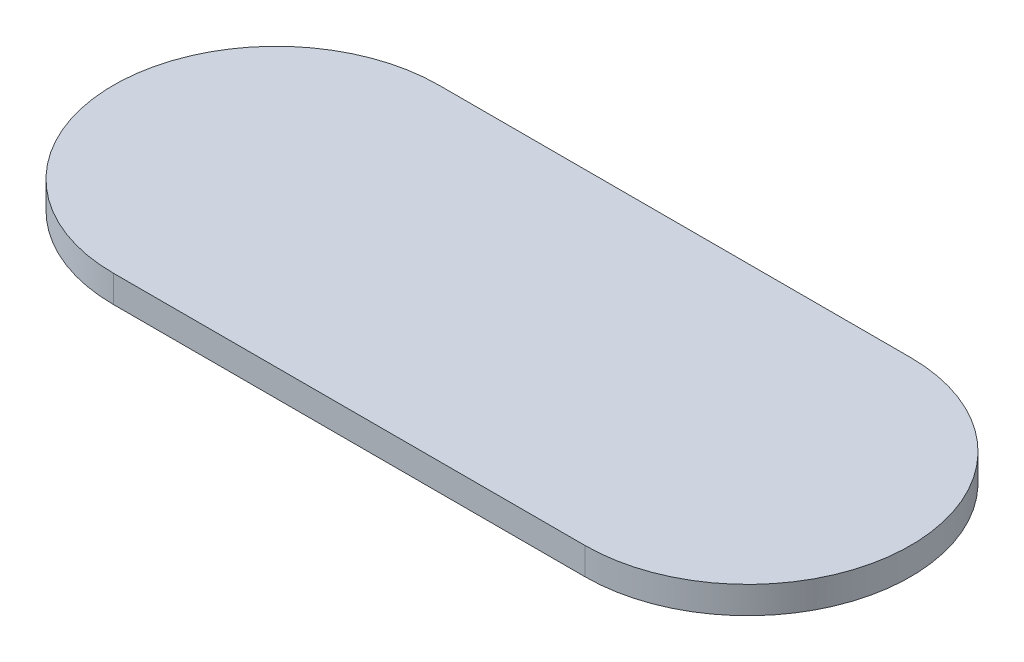
SolidWorks part; units mm, degrees
ref_plane "Front Plane" through (0, 0, 0) normal (0, 0, 1) x (1, 0, 0)
ref_plane "Top Plane" through (0, 0, 0) normal (0, 1, 0) x (1, 0, 0)
ref_plane "Right Plane" through (0, 0, 0) normal (1, 0, 0) x (0, 0, -1)
sketch "Sketch2" plane through (0, 0, 0) normal (0, 1, 0) x (1, 0, 0)
  line L0 (-114.3925, 0) -> (59.4393, 0) construction
  line L1 (-114.3925, 60) -> (59.4393, 60)
  line L2 (-114.3925, -60) -> (59.4393, -60)
  arc A0 (-114.3925, 60) -> (-114.3925, -60) centre (-114.3925, 0) ccw
  arc A1 (59.4393, -60) -> (59.4393, 60) centre (59.4393, 0) ccw
  point P3 (-27.4766, 0)
  dimension "D1" = 60
extrude "Boss-Extrude2" add sketch "Sketch2" along normal blind 10
